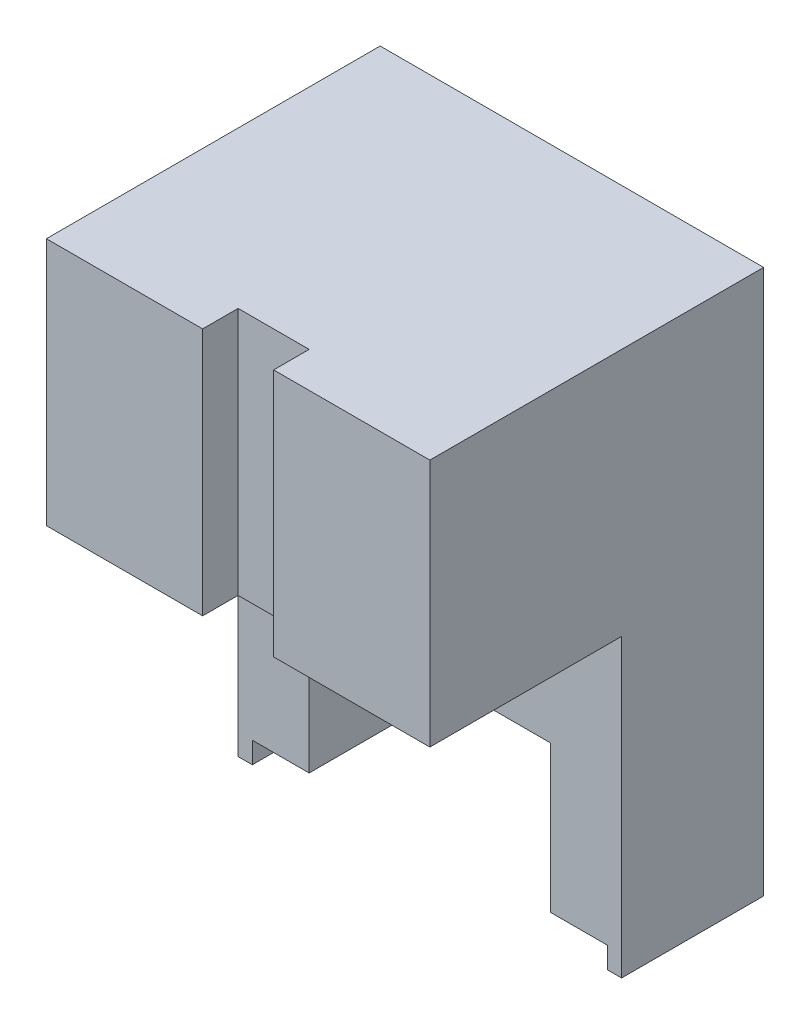
SolidWorks part; units mm, degrees
ref_plane "Plan de face" through (0, 0, 0) normal (0, 0, 1) x (1, 0, 0)
ref_plane "Plan de dessus" through (0, 0, 0) normal (0, 1, 0) x (1, 0, 0)
ref_plane "Plan de droite" through (0, 0, 0) normal (1, 0, 0) x (0, 0, -1)
sketch "Esquisse1" plane through (0, 0, 0) normal (0, 0, 1) x (1, 0, 0)
  line L0 (0, 0) -> (-8, 0)
  line L1 (-50, 0) -> (-50, -3)
  line L2 (-50, -3) -> (-52, -3)
  line L3 (-52, -3) -> (-52, 73.66)
  line L4 (-25, 0) -> (-25, 2.66) construction
  line L5 (-25, 2.66) -> (-25, 32.66) construction
  line L6 (-52, -3) -> (-52, 75.66) construction
  line L7 (2, 73.66) -> (-52, 73.66)
  line L8 (-42, 0) -> (-42, 20.66)
  line L10 (-42, -3) -> (-42, 75.66) construction
  line L11 (-8, 0) -> (-8, 20.66)
  line L12 (2, -3) -> (2, 73.66)
  line L13 (0, -3) -> (2, -3)
  line L14 (0, 0) -> (0, -3)
  line L15 (-42, 0) -> (-50, 0)
  line L17 (-8, 20.66) -> (-42, 20.66)
  circle A0 centre (-25, 2.66) radius 30 construction
  circle A1 centre (-25, 2.66) radius 15 construction
extrude "Extrusion1" add sketch "Esquisse1" along normal blind 20
sketch "Esquisse2" plane through (0, 0, 20) normal (0, 0, 1) x (1, 0, 0)
  line L0 (-52, 38.66) -> (2, 38.66)
  line L2 (-52, 73.66) -> (-52, 38.66)
  line L4 (-52, 73.66) -> (2, 73.66)
  line L6 (2, 38.66) -> (2, 73.66)
extrude "Extrusion2" add sketch "Esquisse2" along normal blind 27
sketch "Esquisse4" plane through (0, 73.66, 0) normal (0, 1, 0) x (1, 0, 0)
  line L0 (-25, -47) -> (-25, -42) construction
  line L1 (2, -47) -> (-52, -47) construction
  line L2 (-30, -42) -> (-20, -42)
  line L3 (-20, -42) -> (-20, -47)
  line L4 (-30, -47) -> (-20, -47)
  line L5 (-30, -42) -> (-30, -47)
extrude "Extrusion4" cut sketch "Esquisse4" against normal through all
